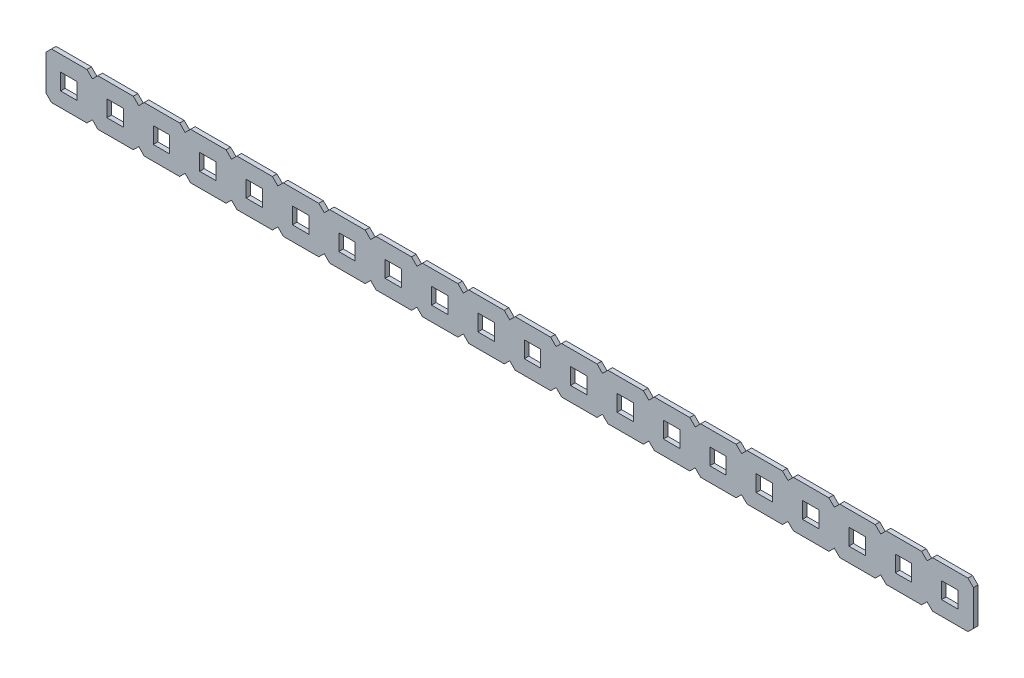
SolidWorks part; units mm, degrees
ref_plane "Front Plane" through (0, 0, 0) normal (0, 0, 1) x (1, 0, 0)
ref_plane "Top Plane" through (0, 0, 0) normal (0, 1, 0) x (1, 0, 0)
ref_plane "Right Plane" through (0, 0, 0) normal (1, 0, 0) x (0, 0, -1)
sketch "Sketch1" plane through (0, 0, 0) normal (0, 0, 1) x (1, 0, 0)
  line L1 (0, 0) -> (319, 0)
  line L2 (0, 0) -> (0, 12.75)
  line L3 (0, 12.75) -> (319, 12.75)
  line L4 (319, 0) -> (319, 12.75)
  dimension "D1" = 12.75
  dimension "D2" = 319
extrude "Boss-Extrude1" add sketch "Sketch1" along normal blind 1.25
sketch "Sketch2" plane through (0, 0, 1.25) normal (0, 0, 1) x (1, 0, 0)
  line L0 (0, 12.75) -> (0, 0) construction
  line L1 (4, 8.5) -> (8.5, 8.5)
  line L2 (4, 8.5) -> (4, 4)
  line L3 (4, 4) -> (8.5, 4)
  line L4 (8.5, 8.5) -> (8.5, 4)
  line L5 (0, 0) -> (319, 0) construction
  line L6 (0, 1.5) -> (1.5, 0)
  line L7 (319, 12.75) -> (0, 12.75) construction
  line L8 (0, 11.25) -> (0, 1.5)
  line L9 (0, 11.25) -> (1.5, 12.75)
  line L10 (12.75, 11.25) -> (11.25, 12.75)
  line L11 (12.75, 1.5) -> (11.25, 0)
  line L12 (12.75, 11.25) -> (12.75, 1.5)
  line L13 (1.5, 12.75) -> (11.25, 12.75)
  line L14 (1.5, 0) -> (11.25, 0)
  line L15 (14.25, 12.75) -> (24, 12.75)
  line L16 (12.75, 11.25) -> (14.25, 12.75)
  line L17 (12.75, 11.25) -> (12.75, 1.5)
  line L18 (12.75, 1.5) -> (14.25, 0)
  line L19 (14.25, 0) -> (24, 0)
  line L20 (25.5, 1.5) -> (24, 0)
  line L21 (25.5, 11.25) -> (25.5, 1.5)
  line L22 (25.5, 11.25) -> (24, 12.75)
  line L23 (16.75, 8.5) -> (16.75, 4)
  line L24 (16.75, 8.5) -> (21.25, 8.5)
  line L25 (21.25, 8.5) -> (21.25, 4)
  line L26 (16.75, 4) -> (21.25, 4)
  line L27 (27, 12.75) -> (36.75, 12.75)
  line L28 (25.5, 11.25) -> (27, 12.75)
  line L29 (25.5, 11.25) -> (25.5, 1.5)
  line L30 (25.5, 1.5) -> (27, 0)
  line L31 (27, 0) -> (36.75, 0)
  line L32 (38.25, 1.5) -> (36.75, 0)
  line L33 (38.25, 11.25) -> (38.25, 1.5)
  line L34 (38.25, 11.25) -> (36.75, 12.75)
  line L35 (29.5, 8.5) -> (29.5, 4)
  line L36 (29.5, 8.5) -> (34, 8.5)
  line L37 (34, 8.5) -> (34, 4)
  line L38 (29.5, 4) -> (34, 4)
  line L39 (39.75, 12.75) -> (49.5, 12.75)
  line L40 (38.25, 11.25) -> (39.75, 12.75)
  line L41 (38.25, 11.25) -> (38.25, 1.5)
  line L42 (38.25, 1.5) -> (39.75, 0)
  line L43 (39.75, 0) -> (49.5, 0)
  line L44 (51, 1.5) -> (49.5, 0)
  line L45 (51, 11.25) -> (51, 1.5)
  line L46 (51, 11.25) -> (49.5, 12.75)
  line L47 (42.25, 8.5) -> (42.25, 4)
  line L48 (42.25, 8.5) -> (46.75, 8.5)
  line L49 (46.75, 8.5) -> (46.75, 4)
  line L50 (42.25, 4) -> (46.75, 4)
  line L51 (52.5, 12.75) -> (62.25, 12.75)
  line L52 (51, 11.25) -> (52.5, 12.75)
  line L53 (51, 11.25) -> (51, 1.5)
  line L54 (51, 1.5) -> (52.5, 0)
  line L55 (52.5, 0) -> (62.25, 0)
  line L56 (63.75, 1.5) -> (62.25, 0)
  line L57 (63.75, 11.25) -> (63.75, 1.5)
  line L58 (63.75, 11.25) -> (62.25, 12.75)
  line L59 (55, 8.5) -> (55, 4)
  line L60 (55, 8.5) -> (59.5, 8.5)
  line L61 (59.5, 8.5) -> (59.5, 4)
  line L62 (55, 4) -> (59.5, 4)
  line L63 (65.25, 12.75) -> (75, 12.75)
  line L64 (63.75, 11.25) -> (65.25, 12.75)
  line L65 (63.75, 11.25) -> (63.75, 1.5)
  line L66 (63.75, 1.5) -> (65.25, 0)
  line L67 (65.25, 0) -> (75, 0)
  line L68 (76.5, 1.5) -> (75, 0)
  line L69 (76.5, 11.25) -> (76.5, 1.5)
  line L70 (76.5, 11.25) -> (75, 12.75)
  line L71 (67.75, 8.5) -> (67.75, 4)
  line L72 (67.75, 8.5) -> (72.25, 8.5)
  line L73 (72.25, 8.5) -> (72.25, 4)
  line L74 (67.75, 4) -> (72.25, 4)
  line L75 (78, 12.75) -> (87.75, 12.75)
  line L76 (76.5, 11.25) -> (78, 12.75)
  line L77 (76.5, 11.25) -> (76.5, 1.5)
  line L78 (76.5, 1.5) -> (78, 0)
  line L79 (78, 0) -> (87.75, 0)
  line L80 (89.25, 1.5) -> (87.75, 0)
  line L81 (89.25, 11.25) -> (89.25, 1.5)
  line L82 (89.25, 11.25) -> (87.75, 12.75)
  line L83 (80.5, 8.5) -> (80.5, 4)
  line L84 (80.5, 8.5) -> (85, 8.5)
  line L85 (85, 8.5) -> (85, 4)
  line L86 (80.5, 4) -> (85, 4)
  line L87 (90.75, 12.75) -> (100.5, 12.75)
  line L88 (89.25, 11.25) -> (90.75, 12.75)
  line L89 (89.25, 11.25) -> (89.25, 1.5)
  line L90 (89.25, 1.5) -> (90.75, 0)
  line L91 (90.75, 0) -> (100.5, 0)
  line L92 (102, 1.5) -> (100.5, 0)
  line L93 (102, 11.25) -> (102, 1.5)
  line L94 (102, 11.25) -> (100.5, 12.75)
  line L95 (93.25, 8.5) -> (93.25, 4)
  line L96 (93.25, 8.5) -> (97.75, 8.5)
  line L97 (97.75, 8.5) -> (97.75, 4)
  line L98 (93.25, 4) -> (97.75, 4)
  line L99 (103.5, 12.75) -> (113.25, 12.75)
  line L100 (102, 11.25) -> (103.5, 12.75)
  line L101 (102, 11.25) -> (102, 1.5)
  line L102 (102, 1.5) -> (103.5, 0)
  line L103 (103.5, 0) -> (113.25, 0)
  line L104 (114.75, 1.5) -> (113.25, 0)
  line L105 (114.75, 11.25) -> (114.75, 1.5)
  line L106 (114.75, 11.25) -> (113.25, 12.75)
  line L107 (106, 8.5) -> (106, 4)
  line L108 (106, 8.5) -> (110.5, 8.5)
  line L109 (110.5, 8.5) -> (110.5, 4)
  line L110 (106, 4) -> (110.5, 4)
  line L111 (116.25, 12.75) -> (126, 12.75)
  line L112 (114.75, 11.25) -> (116.25, 12.75)
  line L113 (114.75, 11.25) -> (114.75, 1.5)
  line L114 (114.75, 1.5) -> (116.25, 0)
  line L115 (116.25, 0) -> (126, 0)
  line L116 (127.5, 1.5) -> (126, 0)
  line L117 (127.5, 11.25) -> (127.5, 1.5)
  line L118 (127.5, 11.25) -> (126, 12.75)
  line L119 (118.75, 8.5) -> (118.75, 4)
  line L120 (118.75, 8.5) -> (123.25, 8.5)
  line L121 (123.25, 8.5) -> (123.25, 4)
  line L122 (118.75, 4) -> (123.25, 4)
  line L123 (129, 12.75) -> (138.75, 12.75)
  line L124 (127.5, 11.25) -> (129, 12.75)
  line L125 (127.5, 11.25) -> (127.5, 1.5)
  line L126 (127.5, 1.5) -> (129, 0)
  line L127 (129, 0) -> (138.75, 0)
  line L128 (140.25, 1.5) -> (138.75, 0)
  line L129 (140.25, 11.25) -> (140.25, 1.5)
  line L130 (140.25, 11.25) -> (138.75, 12.75)
  line L131 (131.5, 8.5) -> (131.5, 4)
  line L132 (131.5, 8.5) -> (136, 8.5)
  line L133 (136, 8.5) -> (136, 4)
  line L134 (131.5, 4) -> (136, 4)
  line L135 (141.75, 12.75) -> (151.5, 12.75)
  line L136 (140.25, 11.25) -> (141.75, 12.75)
  line L137 (140.25, 11.25) -> (140.25, 1.5)
  line L138 (140.25, 1.5) -> (141.75, 0)
  line L139 (141.75, 0) -> (151.5, 0)
  line L140 (153, 1.5) -> (151.5, 0)
  line L141 (153, 11.25) -> (153, 1.5)
  line L142 (153, 11.25) -> (151.5, 12.75)
  line L143 (144.25, 8.5) -> (144.25, 4)
  line L144 (144.25, 8.5) -> (148.75, 8.5)
  line L145 (148.75, 8.5) -> (148.75, 4)
  line L146 (144.25, 4) -> (148.75, 4)
  line L147 (154.5, 12.75) -> (164.25, 12.75)
  line L148 (153, 11.25) -> (154.5, 12.75)
  line L149 (153, 11.25) -> (153, 1.5)
  line L150 (153, 1.5) -> (154.5, 0)
  line L151 (154.5, 0) -> (164.25, 0)
  line L152 (165.75, 1.5) -> (164.25, 0)
  line L153 (165.75, 11.25) -> (165.75, 1.5)
  line L154 (165.75, 11.25) -> (164.25, 12.75)
  line L155 (157, 8.5) -> (157, 4)
  line L156 (157, 8.5) -> (161.5, 8.5)
  line L157 (161.5, 8.5) -> (161.5, 4)
  line L158 (157, 4) -> (161.5, 4)
  line L159 (167.25, 12.75) -> (177, 12.75)
  line L160 (165.75, 11.25) -> (167.25, 12.75)
  line L161 (165.75, 11.25) -> (165.75, 1.5)
  line L162 (165.75, 1.5) -> (167.25, 0)
  line L163 (167.25, 0) -> (177, 0)
  line L164 (178.5, 1.5) -> (177, 0)
  line L165 (178.5, 11.25) -> (178.5, 1.5)
  line L166 (178.5, 11.25) -> (177, 12.75)
  line L167 (169.75, 8.5) -> (169.75, 4)
  line L168 (169.75, 8.5) -> (174.25, 8.5)
  line L169 (174.25, 8.5) -> (174.25, 4)
  line L170 (169.75, 4) -> (174.25, 4)
  line L171 (180, 12.75) -> (189.75, 12.75)
  line L172 (178.5, 11.25) -> (180, 12.75)
  line L173 (178.5, 11.25) -> (178.5, 1.5)
  line L174 (178.5, 1.5) -> (180, 0)
  line L175 (180, 0) -> (189.75, 0)
  line L176 (191.25, 1.5) -> (189.75, 0)
  line L177 (191.25, 11.25) -> (191.25, 1.5)
  line L178 (191.25, 11.25) -> (189.75, 12.75)
  line L179 (182.5, 8.5) -> (182.5, 4)
  line L180 (182.5, 8.5) -> (187, 8.5)
  line L181 (187, 8.5) -> (187, 4)
  line L182 (182.5, 4) -> (187, 4)
  line L183 (192.75, 12.75) -> (202.5, 12.75)
  line L184 (191.25, 11.25) -> (192.75, 12.75)
  line L185 (191.25, 11.25) -> (191.25, 1.5)
  line L186 (191.25, 1.5) -> (192.75, 0)
  line L187 (192.75, 0) -> (202.5, 0)
  line L188 (204, 1.5) -> (202.5, 0)
  line L189 (204, 11.25) -> (204, 1.5)
  line L190 (204, 11.25) -> (202.5, 12.75)
  line L191 (195.25, 8.5) -> (195.25, 4)
  line L192 (195.25, 8.5) -> (199.75, 8.5)
  line L193 (199.75, 8.5) -> (199.75, 4)
  line L194 (195.25, 4) -> (199.75, 4)
  line L195 (205.5, 12.75) -> (215.25, 12.75)
  line L196 (204, 11.25) -> (205.5, 12.75)
  line L197 (204, 11.25) -> (204, 1.5)
  line L198 (204, 1.5) -> (205.5, 0)
  line L199 (205.5, 0) -> (215.25, 0)
  line L200 (216.75, 1.5) -> (215.25, 0)
  line L201 (216.75, 11.25) -> (216.75, 1.5)
  line L202 (216.75, 11.25) -> (215.25, 12.75)
  line L203 (208, 8.5) -> (208, 4)
  line L204 (208, 8.5) -> (212.5, 8.5)
  line L205 (212.5, 8.5) -> (212.5, 4)
  line L206 (208, 4) -> (212.5, 4)
  line L207 (218.25, 12.75) -> (228, 12.75)
  line L208 (216.75, 11.25) -> (218.25, 12.75)
  line L209 (216.75, 11.25) -> (216.75, 1.5)
  line L210 (216.75, 1.5) -> (218.25, 0)
  line L211 (218.25, 0) -> (228, 0)
  line L212 (229.5, 1.5) -> (228, 0)
  line L213 (229.5, 11.25) -> (229.5, 1.5)
  line L214 (229.5, 11.25) -> (228, 12.75)
  line L215 (220.75, 8.5) -> (220.75, 4)
  line L216 (220.75, 8.5) -> (225.25, 8.5)
  line L217 (225.25, 8.5) -> (225.25, 4)
  line L218 (220.75, 4) -> (225.25, 4)
  line L219 (231, 12.75) -> (240.75, 12.75)
  line L220 (229.5, 11.25) -> (231, 12.75)
  line L221 (229.5, 11.25) -> (229.5, 1.5)
  line L222 (229.5, 1.5) -> (231, 0)
  line L223 (231, 0) -> (240.75, 0)
  line L224 (242.25, 1.5) -> (240.75, 0)
  line L225 (242.25, 11.25) -> (242.25, 1.5)
  line L226 (242.25, 11.25) -> (240.75, 12.75)
  line L227 (233.5, 8.5) -> (233.5, 4)
  line L228 (233.5, 8.5) -> (238, 8.5)
  line L229 (238, 8.5) -> (238, 4)
  line L230 (233.5, 4) -> (238, 4)
  line L231 (243.75, 12.75) -> (253.5, 12.75)
  line L232 (242.25, 11.25) -> (243.75, 12.75)
  line L233 (242.25, 11.25) -> (242.25, 1.5)
  line L234 (242.25, 1.5) -> (243.75, 0)
  line L235 (243.75, 0) -> (253.5, 0)
  line L236 (255, 1.5) -> (253.5, 0)
  line L237 (255, 11.25) -> (255, 1.5)
  line L238 (255, 11.25) -> (253.5, 12.75)
  line L239 (246.25, 8.5) -> (246.25, 4)
  line L240 (246.25, 8.5) -> (250.75, 8.5)
  line L241 (250.75, 8.5) -> (250.75, 4)
  line L242 (246.25, 4) -> (250.75, 4)
  line L243 (256.5, 12.75) -> (266.25, 12.75)
  line L244 (255, 11.25) -> (256.5, 12.75)
  line L245 (255, 11.25) -> (255, 1.5)
  line L246 (255, 1.5) -> (256.5, 0)
  line L247 (256.5, 0) -> (266.25, 0)
  line L248 (267.75, 1.5) -> (266.25, 0)
  line L249 (267.75, 11.25) -> (267.75, 1.5)
  line L250 (267.75, 11.25) -> (266.25, 12.75)
  line L251 (259, 8.5) -> (259, 4)
  line L252 (259, 8.5) -> (263.5, 8.5)
  line L253 (263.5, 8.5) -> (263.5, 4)
  line L254 (259, 4) -> (263.5, 4)
  line L255 (269.25, 12.75) -> (279, 12.75)
  line L256 (267.75, 11.25) -> (269.25, 12.75)
  line L257 (267.75, 11.25) -> (267.75, 1.5)
  line L258 (267.75, 1.5) -> (269.25, 0)
  line L259 (269.25, 0) -> (279, 0)
  line L260 (280.5, 1.5) -> (279, 0)
  line L261 (280.5, 11.25) -> (280.5, 1.5)
  line L262 (280.5, 11.25) -> (279, 12.75)
  line L263 (271.75, 8.5) -> (271.75, 4)
  line L264 (271.75, 8.5) -> (276.25, 8.5)
  line L265 (276.25, 8.5) -> (276.25, 4)
  line L266 (271.75, 4) -> (276.25, 4)
  line L267 (282, 12.75) -> (291.75, 12.75)
  line L268 (280.5, 11.25) -> (282, 12.75)
  line L269 (280.5, 11.25) -> (280.5, 1.5)
  line L270 (280.5, 1.5) -> (282, 0)
  line L271 (282, 0) -> (291.75, 0)
  line L272 (293.25, 1.5) -> (291.75, 0)
  line L273 (293.25, 11.25) -> (293.25, 1.5)
  line L274 (293.25, 11.25) -> (291.75, 12.75)
  line L275 (284.5, 8.5) -> (284.5, 4)
  line L276 (284.5, 8.5) -> (289, 8.5)
  line L277 (289, 8.5) -> (289, 4)
  line L278 (284.5, 4) -> (289, 4)
  line L279 (294.75, 12.75) -> (304.5, 12.75)
  line L280 (293.25, 11.25) -> (294.75, 12.75)
  line L281 (293.25, 11.25) -> (293.25, 1.5)
  line L282 (293.25, 1.5) -> (294.75, 0)
  line L283 (294.75, 0) -> (304.5, 0)
  line L284 (306, 1.5) -> (304.5, 0)
  line L285 (306, 11.25) -> (306, 1.5)
  line L286 (306, 11.25) -> (304.5, 12.75)
  line L287 (297.25, 8.5) -> (297.25, 4)
  line L288 (297.25, 8.5) -> (301.75, 8.5)
  line L289 (301.75, 8.5) -> (301.75, 4)
  line L290 (297.25, 4) -> (301.75, 4)
  line L291 (307.5, 12.75) -> (317.25, 12.75)
  line L292 (306, 11.25) -> (307.5, 12.75)
  line L293 (306, 11.25) -> (306, 1.5)
  line L294 (306, 1.5) -> (307.5, 0)
  line L295 (307.5, 0) -> (317.25, 0)
  line L296 (318.75, 1.5) -> (317.25, 0)
  line L297 (318.75, 11.25) -> (318.75, 1.5)
  line L298 (318.75, 11.25) -> (317.25, 12.75)
  line L299 (310, 8.5) -> (310, 4)
  line L300 (310, 8.5) -> (314.5, 8.5)
  line L301 (314.5, 8.5) -> (314.5, 4)
  line L302 (310, 4) -> (314.5, 4)
  point P6 (4, 6.25)
  line M12 (0, 12.75) -> (0, 0)
  line M13 (0, 0) -> (319, 0)
  line M14 (319, 0) -> (319, 12.75)
  line M15 (319, 12.75) -> (0, 12.75)
  dimension "D1" = 4
  dimension "D2" = 4.5
  dimension "D3" = 4.5
  dimension "D4" = 4
  dimension "D5" = 1.5
  dimension "D6" = 1.5
  dimension "D7" = 12.75
  dimension "D8" = 12.75
  dimension "D9" = 1.5
  dimension "D10" = 25
extrude "Cut-Extrude1" cut sketch "Sketch2" against normal blind 18.25 contours L4 L1 L2 L3 | L23 L26 L25 L24 | L35 L38 L37 L36 | L47 L50 L49 L48 | L59 L62 L61 L60 | L71 L74 L73 L72 | L83 L86 L85 L84 | L95 L98 L97 L96 | L107 L110 L109 L108 | L131 L134 L133 L132 | L143 L146 L145 L144 | L167 L170 L169 L168 | L179 L182 L181 L180 | L203 L206 L205 L204 | L215 L218 L217 L216 | L227 L230 L229 L228 | L239 L242 L241 L240 | L251 L254 L253 L252 | L263 L266 L265 L264 | L275 L278 L277 L276 | L287 L290 L289 L288 | L299 L302 L301 L300 | L9 M12 M15 | L6 M12 M13 | L10 L16 M15 | L18 L11 M13 | L30 L20 M13 | L22 L28 M15 | L42 L32 M13 | L46 L52 M15 | L54 L44 M13 | L34 L40 M15 | L58 L64 M15 | L66 L56 M13 | L78 L68 M13 | L70 L76 M15 | L82 L88 M15 | L90 L80 M13 | L102 L92 M13 | L94 L100 M15 | L106 L112 M15 | L114 L104 M13 | L126 L116 M13 | L118 L124 M15 | L138 L128 M13 | L130 L136 M15 | L142 L148 M15 | L150 L140 M13 | L154 L160 M15 | L166 L172 M15 | L178 L184 M15 | L190 L196 M15 | L202 L208 M15 | L214 L220 M15 | L226 L232 M15 | L238 L244 M15 | L250 L256 M15 | L262 L268 M15 | L274 L280 M15 | L286 L292 M15 | L298 L297 L296 M13 M14 M15 | L294 L284 M13 | L282 L272 M13 | L270 L260 M13 | L258 L248 M13 | L246 L236 M13 | L234 L224 M13 | L222 L212 M13 | L162 L152 M13 | L174 L164 M13 | L186 L176 M13 | L198 L188 M13 | L210 L200 M13 | L119 L122 L121 L120 | L193 L194 L191 L192
sketch "Sketch3" plane through (0, 0, 1.25) normal (0, 0, 1) x (1, 0, 0)
  line L0 (157, 8.5) -> (157, 4)
  line L1 (144.25, 8.5) -> (148.75, 8.5)
  line L2 (144.25, 8.5) -> (144.25, 4)
  line L3 (144.25, 4) -> (148.75, 4)
  line L4 (148.75, 8.5) -> (148.75, 4)
  line L5 (157, 8.5) -> (161.5, 8.5)
  line L6 (161.5, 8.5) -> (161.5, 4)
  line L7 (157, 4) -> (161.5, 4)
  dimension "D1" = 2
extrude "Cut-Extrude2" cut sketch "Sketch3" against normal blind 18.25
sketch "Sketch4" plane through (0, 0, 1.25) normal (0, 0, 1) x (1, 0, 0)
  line L0 (255, 11.25) -> (255, 1.5)
  line L2 (255, 14.3295) -> (322.8557, 14.3295)
  line L3 (255, 14.3295) -> (255, -2.3495)
  line L4 (255, -2.3495) -> (322.8557, -2.3495)
  line L5 (322.8557, 14.3295) -> (322.8557, -2.3495)
extrude "Cut-Extrude3" cut sketch "Sketch4" against normal blind 18.25 contours L5 L2 L3 L0 L4
